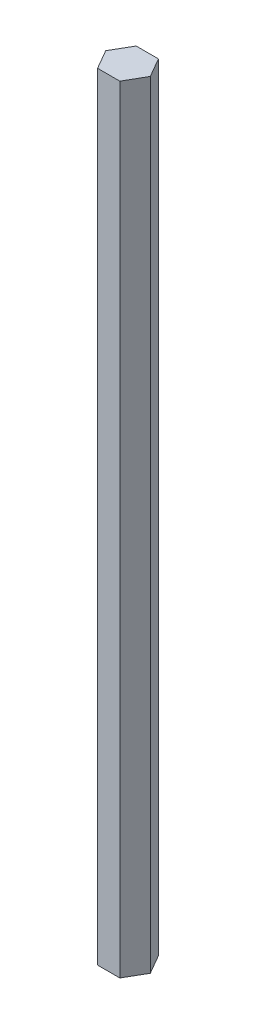
SolidWorks part; units mm, degrees
ref_plane "Front Plane" through (0, 0, 0) normal (0, 0, 1) x (1, 0, 0)
ref_plane "Top Plane" through (0, 0, 0) normal (0, 1, 0) x (1, 0, 0)
ref_plane "Right Plane" through (0, 0, 0) normal (1, 0, 0) x (0, 0, -1)
sketch "Sketch1" plane through (0, 0, 0) normal (0, 1, 0) x (1, 0, 0)
  line L1 (7.3323, 0) -> (3.6662, 6.35)
  line L2 (3.6662, 6.35) -> (-3.6662, 6.35)
  line L3 (-3.6662, 6.35) -> (-7.3323, 0)
  line L4 (-7.3323, 0) -> (-3.6662, -6.35)
  line L5 (-3.6662, -6.35) -> (3.6662, -6.35)
  line L6 (3.6662, -6.35) -> (7.3323, 0)
  circle A0 centre (0, 0) radius 6.35 construction
  dimension "D1" = 12.7
extrude "Boss-Extrude1" add sketch "Sketch1" along normal mid plane 255.65
